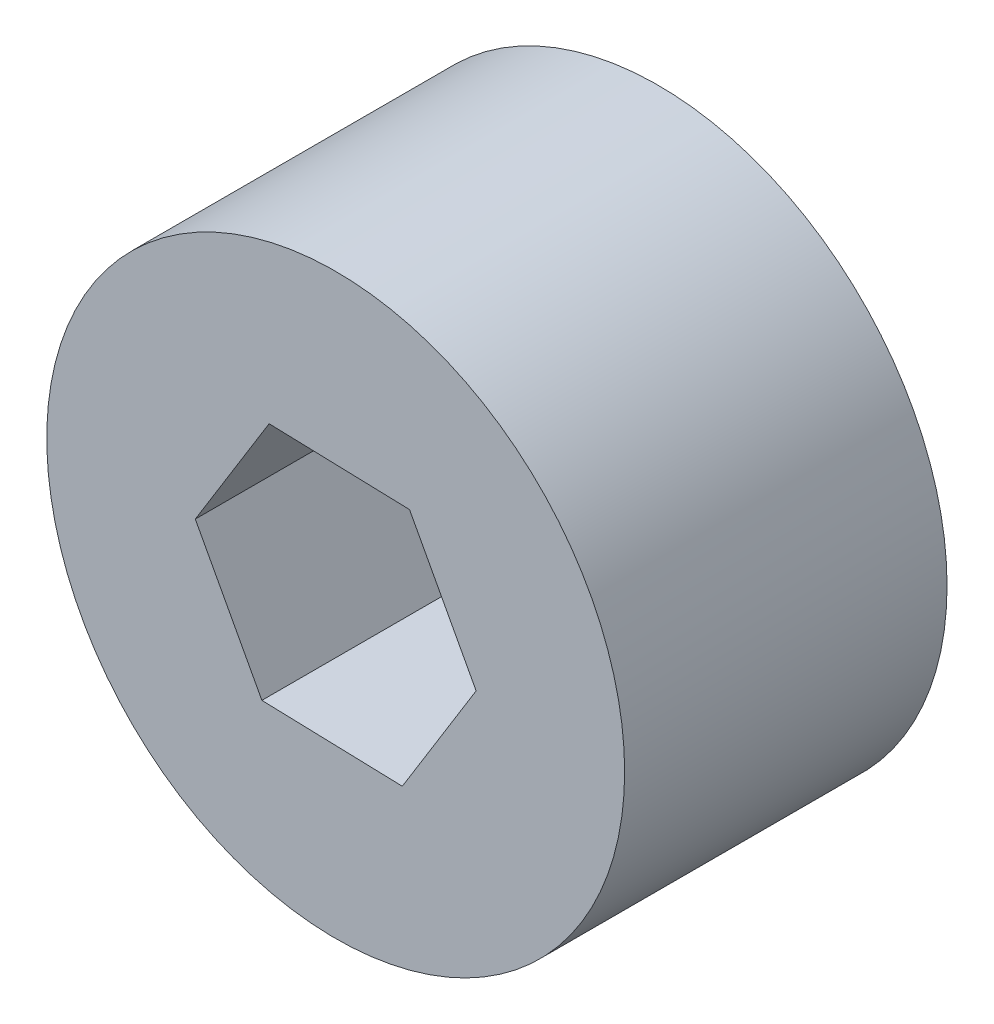
SolidWorks part; units mm, degrees
ref_plane "Front Plane" through (0, 0, 0) normal (0, 0, 1) x (1, 0, 0)
ref_plane "Top Plane" through (0, 0, 0) normal (0, 1, 0) x (1, 0, 0)
ref_plane "Right Plane" through (0, 0, 0) normal (1, 0, 0) x (0, 0, -1)
sketch "Sketch1" plane through (0, 0, 0) normal (0, 0, 1) x (1, 0, 0)
  line L1 (3.8531, 6.2383) -> (-3.476, 6.4561)
  line L2 (-3.476, 6.4561) -> (-7.3291, 0.2177)
  line L3 (-7.3291, 0.2177) -> (-3.8531, -6.2383)
  line L4 (-3.8531, -6.2383) -> (3.476, -6.4561)
  line L5 (3.476, -6.4561) -> (7.3291, -0.2177)
  line L6 (7.3291, -0.2177) -> (3.8531, 6.2383)
  circle A0 centre (0, 0) radius 15.0813
  circle A1 centre (0, 0) radius 6.35 construction
  dimension "D1" = 30.1625
  dimension "D2" = 12.7
extrude "Boss-Extrude1" add sketch "Sketch1" along normal blind 16.8275
